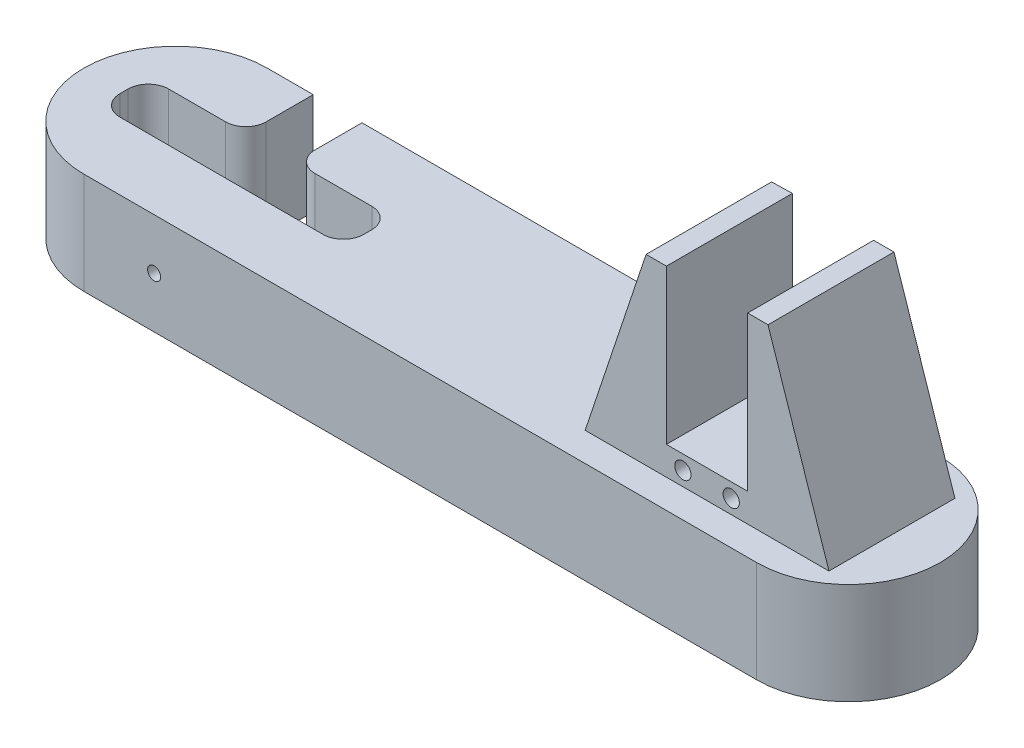
SolidWorks part; units mm, degrees
ref_plane "前基準面" through (0, 0, 0) normal (0, 0, 1) x (1, 0, 0)
ref_plane "上基準面" through (0, 0, 0) normal (0, 1, 0) x (1, 0, 0)
ref_plane "右基準面" through (0, 0, 0) normal (1, 0, 0) x (0, 0, -1)
sketch "草圖1" plane through (0, 0, 0) normal (0, 0, 1) x (1, 0, 0)
  line L0 (0, 0) -> (0, -11.05)
  line L1 (-10, 0) -> (-10, -30.2764)
  line L3 (10, -30.2764) -> (10, 0)
  line L4 (-10, -30.2764) -> (10, -30.2764)
  circle A1 centre (0, 0) radius 1.985
  arc A2 (10, 0) -> (-10, 0) centre (0, 0) ccw
  dimension "D1" = 11.05
  dimension "D2" = 3.97
  dimension "D3" = 20
extrude "填料-伸長1" add sketch "草圖1" along normal blind 12
sketch "草圖2" plane through (10, 0, 0) normal (1, 0, 0) x (0, 0, -1)
  line L0 (-12, 0) -> (-9.1, 0)
  line L1 (-12, 0) -> (0, 0) construction
  line L2 (-12, 10) -> (-12, 0) construction
  line L3 (0, 0) -> (-2.9, 0)
  line L4 (-6, 0) -> (-3, 0)
  line L5 (-6, 0) -> (-9, 0)
  line L6 (-9, 0) -> (-9, 15.7808)
  line L7 (-9, 15.7808) -> (-3, 15.7808)
  line L8 (-3, 15.7808) -> (-3, 0)
  line L9 (-3, 0) -> (-3, -20)
  line L10 (-9, 0) -> (-8.6005, -20)
  line L11 (-8.6005, -20) -> (-3, -20)
  line M8 (0, 0) -> (-12, 0)
  dimension "D1" = 2.9
  dimension "D2" = 2.9
  dimension "D3" = 3
  dimension "D4" = 3
  dimension "D5" = 20
extrude "除料-伸長1" cut sketch "草圖2" against normal through all contours L8 L7 L6 M8 | L10 L11 L9 M8
sketch "草圖11" plane through (10, 0, 0) normal (1, 0, 0) x (0, 0, -1)
  line L0 (-9, 0) -> (-9, -20)
  line L1 (-9, -20) -> (-8.6005, -20)
  line L2 (-9, 0) -> (-8.6005, -20)
extrude "除料-伸長6" cut sketch "草圖11" against normal through all
sketch "草圖12" plane through (0, 0, 12) normal (0, 0, 1) x (1, 0, 0)
  line L0 (-10, 0) -> (-10, -30.2764)
  line L1 (-10, -30.2764) -> (10, -30.2764)
  line L2 (10, -30.2764) -> (10, 0)
  circle A0 centre (0, 0) radius 1.45
  circle A1 centre (0, 0) radius 10
  circle M1 centre (0, 0) radius 1.985
  line M2 (10, -30.2764) -> (10, 0)
  arc M3 (10, 0) -> (-10, 0) centre (0, 0) ccw
  line M4 (-10, 0) -> (-10, -30.2764)
  line M5 (-10, -30.2764) -> (10, -30.2764)
extrude "填料-伸長11" add sketch "草圖12" along normal blind 5 contours A1 M3 M1 | A1 M4 M5 M2
sketch "草圖13" plane through (0, 0, 0) normal (0, 0, -1) x (-1, 0, 0)
  line L0 (-10, 0) -> (-10, -30.2764)
  line L1 (-10, -30.2764) -> (10, -30.2764)
  line L2 (10, 0) -> (10, -30.2764) construction
  line L3 (10, -30.2764) -> (-10, -30.2764) construction
  line L4 (10, -30.2764) -> (10, 0)
  circle A0 centre (0, 0) radius 1.45
  circle A1 centre (0, 0) radius 10
  circle M1 centre (0, 0) radius 1.985
  line M2 (-10, 0) -> (-10, -30.2764)
  line M3 (-10, -30.2764) -> (10, -30.2764)
  line M4 (10, -30.2764) -> (10, 0)
  arc M5 (10, 0) -> (-10, 0) centre (0, 0) ccw
extrude "填料-伸長12" add sketch "草圖13" along normal blind 5 contours A1 M5 M1 | A1 M2 M3 M4
sketch "草圖14" plane through (-10, 0, 0) normal (-1, 0, 0) x (0, 0, 1)
  line L0 (3, -20) -> (0.96, -20)
  line L1 (0.96, -20) -> (0.96, 10)
  line L2 (3, 10) -> (-5, 10) construction
  line L3 (0.96, 10) -> (3, 10)
  line L5 (3, 10) -> (11.04, 10)
  line L6 (9, -20) -> (11.04, -20)
  line L7 (11.04, -20) -> (11.04, 10)
  line L8 (17, 10) -> (9, 10) construction
  line L9 (0.96, 10) -> (11.04, 10)
  line L10 (11.04, -20) -> (0.96, -20)
  line L11 (0.96, 10) -> (0.96, -20)
  line L12 (0.96, 10) -> (11.04, 10)
  line M7 (9, 0) -> (9, -20)
  line M8 (9, -20) -> (3, -20)
  line M9 (3, -20) -> (3, 0)
  line M10 (3, 0) -> (-5, 0)
  line M14 (17, 0) -> (9, 0)
  dimension "D1" = 2.04
  dimension "D2" = 2.04
extrude "除料-伸長7" cut sketch "草圖14" against normal through all contours L7 L5 L3 L1 M14 M10 M9 M8 M7 | L1 L0 M9 M10 | L6 L7 M14 M7
sketch "草圖15" plane through (0, -30.2764, 0) normal (0, -1, 0) x (1, 0, 0)
  line L0 (-10, 6) -> (10, 6)
  line L1 (-10, 17) -> (-10, -5) construction
  line L2 (10, 17) -> (10, -5) construction
  line L3 (0, 17) -> (0, -5)
  line L4 (-10, 17) -> (10, 17) construction
  line L5 (10, -5) -> (-10, -5) construction
  line L7 (-6, 0) -> (6, 0)
  line L8 (-6, 0) -> (-6, 12)
  line L9 (-6, 12) -> (6, 12)
  line L10 (6, 0) -> (6, 12)
  line L11 (-6, 0) -> (6, 12) construction
  line L12 (-6, 12) -> (6, 0) construction
  point P12 (0, 6)
  dimension "D1" = 12
  dimension "D2" = 12
extrude "填料-伸長13" add sketch "草圖15" along normal blind 100 contours L0 L10 L9 L3 | L9 L8 L0 L3 | L7 L10 L0 L3 | L8 L7 L3 L0
sketch "草圖16" plane through (0, -130.2764, 0) normal (0, -1, 0) x (1, 0, 0)
  line L0 (0, 0) -> (0, 12)
  line L1 (-6, 0) -> (6, 0) construction
  line L2 (-6, 12) -> (6, 12) construction
  line L3 (0.1211, 6) -> (6, 6)
  line L4 (6, 0) -> (6, 12) construction
  line L5 (6, 6) -> (176, 6)
  line L10 (176, 6) -> (176, -54)
  line L11 (176, -54) -> (-61, -54)
  line L12 (-61, -54) -> (-61, 6)
  line L13 (-61, 6) -> (-61, 96)
  line L14 (-61, 96) -> (176, 96)
  line L15 (176, 96) -> (176, 6)
  line L16 (-6, 6) -> (-61, 6)
  line L17 (-6, 0) -> (-6, 12) construction
  point P10 (0, 6)
  dimension "D1" = 170
  dimension "D2" = 55
  dimension "D3" = 60
  dimension "D4" = 90
extrude "填料-伸長14" add sketch "草圖16" along normal blind 25
sketch "草圖17" plane through (0, 0, 12) normal (0, 0, 1) x (1, 0, 0)
  line L0 (0, 0) -> (0, -130.2764)
  line L1 (-6, -130.2764) -> (6, -130.2764) construction
sketch "草圖18" plane through (0, -130.2764, 0) normal (0, 1, 0) x (1, 0, 0)
  line L0 (0, -12) -> (116, -12)
  line L1 (116, -12) -> (137.15, -12)
  line L2 (116, -12) -> (94.85, -12)
  line L15 (0, -12) -> (100, -12)
  line L16 (100, -12) -> (100, -37)
  line L17 (100, -37) -> (90, -37)
  line L18 (100, -37) -> (110, -37)
  line L19 (90, -37) -> (90, -47)
  line L20 (90, -47) -> (110, -47)
  line L21 (110, -47) -> (110, -37)
  dimension "D1" = 100
  dimension "D2" = 25
  dimension "D3" = 10
  dimension "D4" = 10
  dimension "D5" = 10
sketch "草圖30" plane through (0, -130.2764, 0) normal (0, 1, 0) x (1, 0, 0)
  line L0 (0, -12) -> (129, -12)
  line L1 (116, -12) -> (137.15, -12) construction
  line L2 (129, -12) -> (129, -37)
  line L4 (129, -37) -> (139, -37)
  line L5 (129, -37) -> (119, -37)
  line L6 (119, -37) -> (119, -68)
  line L7 (119, -68) -> (139, -68)
  line L8 (139, -68) -> (139, -37)
  dimension "D1" = 129
  dimension "D2" = 10
  dimension "D3" = 10
  dimension "D4" = 31
extrude "填料-伸長19" add sketch "草圖30" along normal blind 7 contours L7 L8 L4 L5 L6
sketch "草圖31" plane through (0, -130.2764, 0) normal (0, 1, 0) x (1, 0, 0)
  line L0 (119, -68) -> (114, -68)
  line L1 (114, -68) -> (114, -37.1297)
  line L2 (114, -37.1297) -> (119, -37)
  line L3 (119, -37) -> (119, -68)
  line L4 (139, -37) -> (139, -68)
  line L5 (139, -68) -> (144, -68)
  line L6 (144, -68) -> (144, -37)
  line L7 (144, -37) -> (139, -37)
  dimension "D1" = 5
  dimension "D2" = 5
extrude "填料-伸長20" add sketch "草圖31" along normal blind 45 contours L3 L0 L1 L2 | L7 L4 L5 L6
sketch "草圖33" plane through (0, 0, 68) normal (0, 0, 1) x (1, 0, 0)
  line L0 (114, -85.2764) -> (99, -130.2764)
  line L1 (0, -130.2764) -> (100, -130.2764) construction
  line L2 (99, -130.2764) -> (114, -130.2764)
  line L3 (0, -130.2764) -> (116, -130.2764) construction
  line L4 (116, -130.2764) -> (94.85, -130.2764) construction
  line L5 (114, -130.2764) -> (114, -85.2764)
  line L6 (144, -85.2764) -> (159, -130.2764)
  line L7 (-61, -130.2764) -> (176, -130.2764) construction
  line L8 (159, -130.2764) -> (144, -130.2764)
  line L9 (144, -85.2764) -> (144, -130.2764) construction
  line M4 (144, -130.2764) -> (144, -85.2764)
  line M10 (114, -85.2764) -> (114, -130.2764)
  dimension "D1" = 15
  dimension "D2" = 15
extrude "填料-伸長21" add sketch "草圖33" against normal blind 31 contours L8 L6 M4 | L0 L2 M10
sketch "草圖35" plane through (0, 0, 37) normal (0, 0, -1) x (-1, 0, 0)
  line L0 (-139, -123.2764) -> (-139, -130.2764)
  line L1 (-119, -130.2764) -> (-159, -130.2764) construction
  line L2 (-139, -130.2764) -> (-119, -130.2764)
  line L3 (-119, -130.2764) -> (-119, -123.2764)
  line L4 (-119, -123.2764) -> (-139, -123.2764)
  line L5 (-139, -126.7764) -> (-119, -126.7764)
  line L6 (-129, -130.2764) -> (-129, -123.2764)
  circle A0 centre (-134.95, -126.7764) radius 2
  circle A1 centre (-123.05, -126.7764) radius 2
  point P15 (-129, -126.7764)
  dimension "D1" = 4
  dimension "D2" = 4
  dimension "D3" = 11.9
  dimension "D4" = 5.95
extrude "除料-伸長16" cut sketch "草圖35" against normal through all contours L5 A0 | L5 A0 | L5 A1 | L5 A1
sketch "草圖37" plane through (0, -130.2764, 0) normal (0, 1, 0) x (1, 0, 0)
  line L0 (129, -68) -> (0, -68)
  line L1 (119, -68) -> (139, -68) construction
  dimension "D1" = 129
sketch "草圖38" plane through (-10, 0, 0) normal (-1, 0, 0) x (0, 0, 1)
  line L0 (0.96, 10) -> (0.76, 10)
  line L1 (0.96, 10) -> (-5, 10) construction
  line L2 (11.04, 10) -> (11.24, 10)
  line L3 (17, 10) -> (11.04, 10) construction
  line L4 (0.76, 10) -> (0.76, -20)
  line L5 (0.76, -20) -> (11.24, -20)
  line L6 (11.24, -20) -> (11.24, 10)
  line L7 (0.76, 10) -> (11.24, 10)
  line M3 (0.96, -20) -> (0.96, 0)
  line M4 (0.96, 0) -> (-5, 0)
  line M8 (17, 0) -> (11.04, 0)
  line M9 (11.04, 0) -> (11.04, -20)
  line M10 (11.04, -20) -> (0.96, -20)
  dimension "D1" = 0.2
  dimension "D2" = 0.2
extrude "除料-伸長18" cut sketch "草圖38" against normal through all contours L7 L0 L4 L6 L2 M4 M3 M10 M9 M8 | L4 L5 M3 M4 | L5 L6 M8 M9
fillet "圓角2" radius 10 4 edges at (176, -142.7764, -54) (176, -142.7764, 96) (-61, -142.7764, -54) (-61, -142.7764, 96)
sketch "草圖39" plane through (0, 0, 0) normal (0, 0, -1) x (-1, 0, 0)
  line L0 (-6, -80.2764) -> (-16, -130.2764)
  line L1 (-6, -130.2764) -> (-6, -30.2764) construction
  line L2 (0, -130.2764) -> (-116, -130.2764) construction
  line L3 (-16, -130.2764) -> (-6, -130.2764)
  line L4 (-6, -130.2764) -> (-6, -80.2764)
  line L6 (6, -80.2764) -> (16, -130.2764)
  line L7 (6, -130.2764) -> (6, -30.2764) construction
  line L8 (-166, -130.2764) -> (51, -130.2764) construction
  line L9 (16, -130.2764) -> (6, -130.2764)
  line L10 (6, -130.2764) -> (6, -80.2764)
  dimension "D1" = 50
  dimension "D2" = 10
  dimension "D3" = 10
extrude "填料-伸長22" add sketch "草圖39" against normal blind 12
sketch "草圖40" plane through (6, 0, 0) normal (1, 0, 0) x (0, 0, -1)
  line L0 (-12, -80.2764) -> (-22, -130.2764)
  line L1 (-12, -130.2764) -> (-37, -130.2764) construction
  line L2 (-22, -130.2764) -> (-12, -130.2764)
  line L3 (-12, 0) -> (-12, -130.2764) construction
  line L4 (-12, -130.2764) -> (-12, -80.2764)
  line L5 (0, -80.2764) -> (11.3032, -130.2764)
  line L6 (-86, -130.2764) -> (44, -130.2764) construction
  line L7 (11.3032, -130.2764) -> (0, -130.2764)
  line L8 (0, -130.2764) -> (0, -80.2764)
  dimension "D1" = 10
extrude "填料-伸長23" add sketch "草圖40" against normal blind 12
sketch "草圖43" plane through (0, -130.2764, 0) normal (0, 1, 0) x (1, 0, 0)
  line L0 (0, -4.6155) -> (135.9213, -56.7097) construction
  line L1 (11.053, 24.2233) -> (146.9743, -27.8709)
  line L2 (-11.053, -33.4544) -> (124.8684, -85.5486)
  line L4 (-74.976, 67.6441) -> (186.8952, 67.6441)
  line L5 (-74.976, 67.6441) -> (-74.976, -109.084)
  line L6 (-74.976, -109.084) -> (186.8952, -109.084)
  line L7 (186.8952, 67.6441) -> (186.8952, -109.084)
  arc A0 (11.053, 24.2233) -> (-11.053, -33.4544) centre (0, -4.6155) ccw
  arc A1 (124.8684, -85.5486) -> (146.9743, -27.8709) centre (135.9213, -56.7097) ccw
  point P2 (67.9607, -30.6626)
sketch "草圖44" plane through (0, -130.2764, 0) normal (0, 1, 0) x (1, 0, 0)
  line L0 (148.3068, -52.5) -> (-17.3111, -52.5) construction
  line L1 (148.3068, -74.8661) -> (-17.3111, -74.8661)
  line L2 (148.3068, -30.1339) -> (-17.3111, -30.1339)
  arc A0 (148.3068, -74.8661) -> (148.3068, -30.1339) centre (148.3068, -52.5) ccw
  arc A1 (-17.3111, -30.1339) -> (-17.3111, -74.8661) centre (-17.3111, -52.5) ccw
  point P2 (65.4979, -52.5)
sketch "草圖45" plane through (0, 0, 12) normal (0, 0, 1) x (1, 0, 0)
  line L1 (-6, -70.2764) -> (6, -70.2764)
  line L2 (-6, -70.2764) -> (-6, -58.2764)
  line L3 (-6, -58.2764) -> (6, -58.2764)
  line L4 (6, -70.2764) -> (6, -58.2764)
  line L5 (-6, -70.2764) -> (6, -58.2764) construction
  line L7 (6, -80.2764) -> (6, -30.2764) construction
  line L8 (6, -70.2764) -> (6, -130.2764)
  line M2 (6, -80.2764) -> (6, -30.2764)
  line M4 (-6, -30.2764) -> (-6, -80.2764)
  dimension "D1" = 12
  dimension "D2" = 60
  dimension "D3" = 12
sketch "草圖46" plane through (0, -130.2764, 0) normal (0, 1, 0) x (1, 0, 0)
  line L0 (-6, -22) -> (-6, -52.5)
  line L1 (148.3068, -52.5) -> (-17.3111, -52.5) construction
  line L2 (-6, -52.5) -> (6, -52.5)
  line L3 (6, -52.5) -> (6, -22)
  line L4 (6, -22) -> (-6, -22)
  line L6 (-6, -58.5) -> (6, -58.5)
  line L7 (-6, -58.5) -> (-6, -46.5)
  line L8 (-6, -46.5) -> (6, -46.5)
  line L9 (6, -58.5) -> (6, -46.5)
  line L10 (-6, -58.5) -> (6, -46.5) construction
  line L11 (-6, -46.5) -> (6, -58.5) construction
  point P9 (0, -52.5)
  dimension "D1" = 12
extrude "填料-伸長24" add sketch "草圖46" along normal blind 72 contours L6 L9 L2 L7 | L8 L0 L2 L3
sketch "草圖48" plane through (6, 0, 0) normal (1, 0, 0) x (0, 0, -1)
  line L0 (-46.5, -58.2764) -> (-12, -58.2764)
  line L1 (-12, 0) -> (-12, -130.2764) construction
extrude "填料-伸長26" add sketch "草圖45" along normal blind 34.5 contours L5 L1 M2 | L5 L3 M4
sketch "草圖50" plane through (-6, 0, 0) normal (-1, 0, 0) x (0, 0, 1)
  line L0 (12, -70.2764) -> (0, -70.2764)
  line L1 (0, -80.2764) -> (0, -30.2764) construction
  line L2 (0, -70.2764) -> (-67.3917, -119.055)
  line L3 (-67.3917, -119.055) -> (-58.5081, -164.3613)
  line L6 (21.2221, -86.4078) -> (12, -70.2764)
  line L7 (21.2221, -86.4078) -> (22, -130.2764)
  line L8 (22, -130.2764) -> (22, -164.3613)
  line L9 (22, -164.3613) -> (-58.5081, -164.3613)
extrude "除料-伸長22" cut sketch "草圖50" against normal through all both and the other way through all
sketch "草圖52" plane through (0, -130.2764, 0) normal (0, 1, 0) x (1, 0, 0)
  line L0 (-17.3111, -52.5) -> (148.3068, -52.5) construction
  line L1 (-17.3111, -29.9202) -> (148.3068, -29.9202)
  line L2 (-17.3111, -75.0798) -> (148.3068, -75.0798)
  line L4 (-80.309, -111.0921) -> (196.5518, -111.0921)
  line L5 (-80.309, -111.0921) -> (-80.309, 6.0921)
  line L6 (-80.309, 6.0921) -> (196.5518, 6.0921)
  line L7 (196.5518, -111.0921) -> (196.5518, 6.0921)
  line L8 (-80.309, -111.0921) -> (196.5518, 6.0921) construction
  line L9 (-80.309, 6.0921) -> (196.5518, -111.0921) construction
  arc A0 (-17.3111, -29.9202) -> (-17.3111, -75.0798) centre (-17.3111, -52.5) ccw
  arc A1 (148.3068, -75.0798) -> (148.3068, -29.9202) centre (148.3068, -52.5) ccw
  point P4 (65.4979, -52.5)
  point P9 (58.1214, -52.5)
extrude "除料-伸長24" cut sketch "草圖52" against normal through all both
sketch "草圖56" plane through (0, 0, 58.5) normal (0, 0, 1) x (1, 0, 0)
  line L0 (-6, -70.2764) -> (6, -58.2764) construction
  circle A0 centre (0, -64.2764) radius 1.7
  dimension "D1" = 3.4
extrude "除料-伸長26" cut sketch "草圖56" against normal through all both contours A0
sketch "草圖57" plane through (-6, 0, 0) normal (-1, 0, 0) x (0, 0, 1)
  line L0 (0, -70.2764) -> (0, -130.2764)
  line L1 (0, -130.2764) -> (47, -130.2764)
  line L2 (47, -130.2764) -> (37, -130.2764) construction
  line L3 (74.8661, -130.2764) -> (30.1339, -130.2764) construction
  line L4 (12, -70.2764) -> (12, -118.2764)
  line L5 (12, 0) -> (12, -130.2764) construction
  line L6 (46.5, -70.2764) -> (0, -70.2764) construction
  line L7 (12, -118.2764) -> (46.5, -118.2764)
  line L8 (46.5, -70.2764) -> (46.5, -130.2764) construction
  line L9 (0, -70.2764) -> (12, -70.2764)
  line L10 (12, -118.2764) -> (45.6518, -118.2764)
  line L11 (46.5, -118.2764) -> (46.5, -130.2764)
  line L12 (46.5, -130.2764) -> (0, -130.2764)
  line M4 (0, -70.2764) -> (46.5, -70.2764)
  line M5 (46.5, -70.2764) -> (46.5, -130.2764)
  dimension "D1" = 48
extrude "填料-伸長27" add sketch "草圖57" against normal blind 12 contours L7 L4 L0 L1 M4 M5
sketch "草圖58" plane through (-6, 0, 0) normal (-1, 0, 0) x (0, 0, 1)
  line L0 (12, -50.3535) -> (12, -118.2764)
  line L1 (12, 0) -> (12, -130.2764) construction
  line L2 (12, -118.2764) -> (97.7174, -118.2764)
  line L3 (97.7174, -118.2764) -> (103.2254, -26.7918)
  line L4 (103.2254, -26.7918) -> (12, -50.3535)
extrude "除料-伸長27" cut sketch "草圖58" against normal blind 12
sketch "草圖59" plane through (0, -130.2764, 0) normal (0, -1, 0) x (1, 0, 0)
  line L0 (-6, 29.9202) -> (-6, 0)
  line L1 (-6, 0) -> (6, 0)
  line L2 (6, 0) -> (6, 29.9202)
  line L3 (6, 29.9202) -> (-6, 29.9202)
extrude "填料-伸長29" add sketch "草圖59" along normal blind 25
sketch "草圖60" plane through (0, -130.2764, 0) normal (0, 1, 0) x (1, 0, 0)
  line L0 (6, -58.5) -> (30, -58.5)
  line L1 (30, -58.5) -> (30, -46.5)
  line L2 (30, -46.5) -> (6, -46.5)
  line L3 (6, -58.5) -> (6, -29.9202) construction
  line L4 (-6, -58.5) -> (-30, -58.5)
  line L5 (-30, -58.5) -> (-30, -46.5)
  line L6 (-30, -46.5) -> (-6, -46.5)
  line L7 (-6, -58.5) -> (-6, -29.9202) construction
  line L9 (-6, -46.5) -> (-6, -58.5)
  line L10 (6, -46.5) -> (6, -58.5)
  dimension "D1" = 12
  dimension "D2" = 24
  dimension "D3" = 24
extrude "填料-伸長30" add sketch "草圖60" along normal blind 12 and the other way blind 25
sketch "草圖61" plane through (0, -130.2764, 0) normal (0, 1, 0) x (1, 0, 0)
  line L2 (-6, -46.5) -> (-30, -46.5)
  line L3 (-30, -46.5) -> (-30, -58.5)
  line L4 (-30, -58.5) -> (30, -58.5)
  line L5 (30, -58.5) -> (30, -46.5)
  line L6 (30, -46.5) -> (6, -46.5)
  line L8 (24.5709, -19.2819) -> (2.9037, 31.9315)
  line L9 (2.9037, 31.9315) -> (-27.0803, 24.0525)
  line L10 (-27.0803, 24.0525) -> (-16.7353, -15.3159)
  line L11 (-16.7353, -15.3159) -> (-15.0707, -21.6504)
  line L14 (-10, -17) -> (-6, -17)
  line L15 (-10, -17) -> (10, -17) construction
  line L16 (-6, -17) -> (-6, -29.9202)
  line L17 (-6, -46.5) -> (-6, -26.7818)
  line L19 (-6, -26.7818) -> (-15.0707, -21.6504)
  line L20 (6, -46.5) -> (6, -25.6276)
  line L21 (6, -12) -> (6, -46.5) construction
  line L22 (6, -25.6276) -> (24.5709, -19.2819)
extrude "除料-伸長29" cut sketch "草圖61" against normal through all both and the other way through all
sketch "草圖63" plane through (0, 0, 58.5) normal (0, 0, -1) x (-1, 0, 0)
  line L0 (30, -130.2764) -> (30, -155.2764)
  line L1 (30, -142.7764) -> (-28.3739, -142.7764)
sketch "草圖64" plane through (0, 0, 58.5) normal (0, 0, -1) x (-1, 0, 0)
  line L0 (30, -142.7764) -> (-28.3739, -142.7764) construction
  line L1 (-6, -130.2764) -> (6, -130.2764)
  line L2 (-6, -130.2764) -> (-6, -155.2764)
  line L3 (-6, -155.2764) -> (6, -155.2764)
  line L4 (6, -130.2764) -> (6, -155.2764)
  circle A0 centre (0, -142.7764) radius 3.1
  dimension "D1" = 6.2
extrude "除料-伸長30" cut sketch "草圖64" against normal blind 3 contours A0
sketch "草圖65" plane through (0, 0, 61.5) normal (0, 0, -1) x (-1, 0, 0)
  circle A0 centre (0, -142.7764) radius 1.6
  dimension "D1" = 3.2
extrude "除料-伸長32" cut sketch "草圖65" against normal through all
fillet "圓角3" radius 5 1 edges at (30, -142.7764, 58.5)
fillet "圓角4" radius 5 5 edges at (-30, -142.7764, 46.5) (-6, -142.7764, 46.5) (6, -142.7764, 46.5) (-30, -142.7764, 58.5) (30, -142.7764, 46.5)
